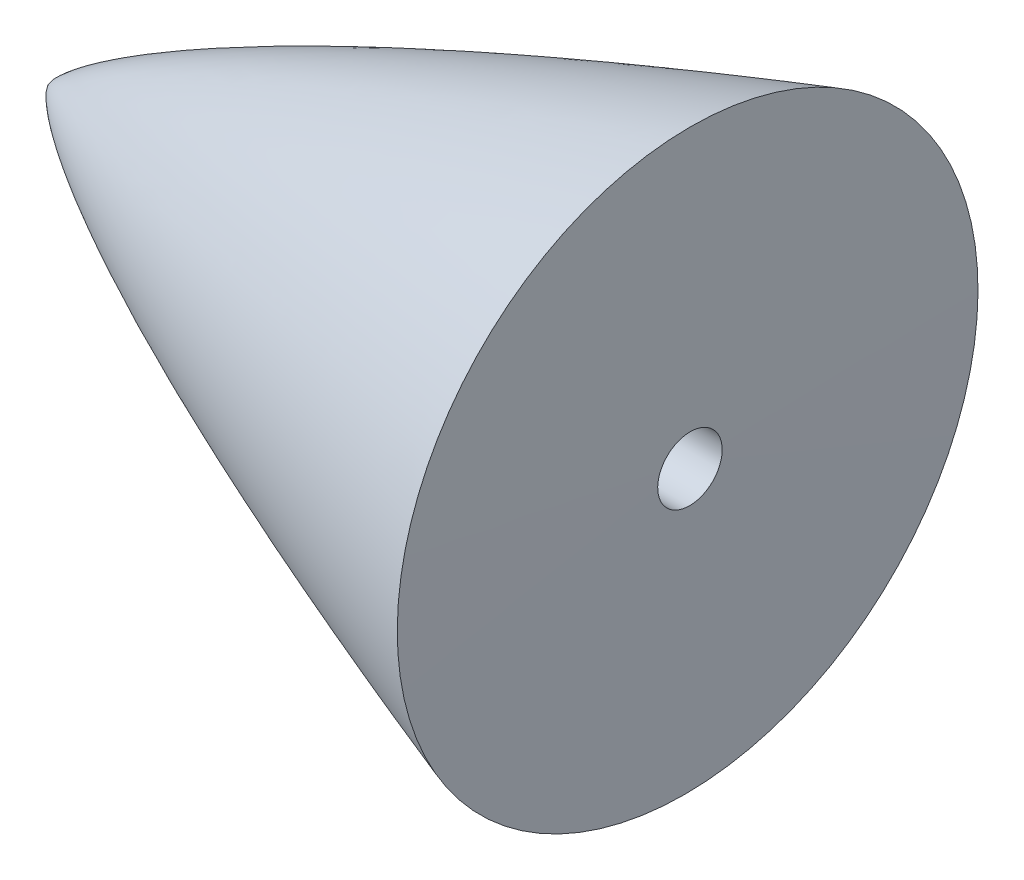
SolidWorks part; units mm, degrees
ref_plane "Front Plane" through (0, 0, 0) normal (0, 0, 1) x (1, 0, 0)
ref_plane "Top Plane" through (0, 0, 0) normal (0, 1, 0) x (1, 0, 0)
ref_plane "Right Plane" through (0, 0, 0) normal (1, 0, 0) x (0, 0, -1)
sketch "Sketch1" plane through (0, 0, 0) normal (0, 0, 1) x (1, 0, 0)
  line L0 (0, 0) -> (50.8, -0.4644)
  line L1 (50.8, -0.4644) -> (50.8, 22.5304)
  spline S0 degree 4 poles (0, 0) (0.0034, 0.018) (0.0111, 0.0443) (0.0276, 0.0824) (0.0564, 0.1398) (0.0969, 0.2096) (0.165, 0.3125) (0.2783, 0.4621) (0.4613, 0.6747) (0.7551, 0.9759) (1.2208, 1.3985) (1.948, 1.9843) (3.0376, 2.7663) (4.6883, 3.8283) (7.0687, 5.2032) (10.0936, 6.7823) (13.6413, 8.4827) (17.4617, 10.1905) (21.314, 11.8194) (25.1956, 13.386) (28.6053, 14.7087) (31.5467, 15.8166) (33.9916, 16.7185) (35.9736, 17.4379) (37.9137, 18.1333) (39.9342, 18.8455) (42.317, 19.6776) (44.945, 20.576) (47.1774, 21.3311) (50.1657, 22.3229) (51.8907, 22.8893) (54.2047, 23.6424) (55.1287, 23.9372) (55.9178, 24.1913) knots 0 0 0 0 0 0.00119 0.001793 0.002702 0.004188 0.006457 0.009843 0.01494 0.022485 0.033904 0.050863 0.075851 0.109982 0.161962 0.230225 0.298488 0.366751 0.435014 0.503277 0.57154 0.605671 0.639803 0.673934 0.708066 0.742197 0.776328 0.844591 0.878723 0.912854 0.956427 1 1 1 1 1 construction
  spline S1 degree 4 poles (0, 0) (0.0034, 0.018) (0.0111, 0.0443) (0.0276, 0.0824) (0.0564, 0.1398) (0.0969, 0.2096) (0.165, 0.3125) (0.2783, 0.4621) (0.4613, 0.6747) (0.7551, 0.9759) (1.2208, 1.3985) (1.948, 1.9843) (3.0376, 2.7663) (4.6883, 3.8283) (7.0687, 5.2032) (10.0936, 6.7823) (13.6413, 8.4827) (17.4617, 10.1905) (21.314, 11.8194) (25.1956, 13.386) (28.6053, 14.7087) (31.5467, 15.8166) (33.9916, 16.7185) (35.9736, 17.4379) (37.9137, 18.1333) (39.9342, 18.8455) (42.317, 19.6776) (44.945, 20.576) (47.1774, 21.3311) (49.4427, 22.0829) (50.3465, 22.3813) (50.8, 22.5304) knots 0 0 0 0 0 0.00119 0.001793 0.002702 0.004188 0.006457 0.009843 0.01494 0.022485 0.033904 0.050863 0.075851 0.109982 0.161962 0.230225 0.298488 0.366751 0.435014 0.503277 0.57154 0.605671 0.639803 0.673934 0.708066 0.742197 0.776328 0.844591 0.878723 0.912854 0.912854 0.912854 0.912854 0.912854
  point P0 (0, 0)
  dimension "D1" = 50.8
  dimension "D2" = 22.9948
revolve "Revolve3" add sketch "Sketch1" angle 360 about L0
ref_plane "Plane1" through (50.7915, -0.9288, 0) normal (0.9998, -0.0183, 0) x (0, 0, -1)
sketch "Sketch3" plane through (50.7915, -0.9288, 0) normal (0.9998, -0.0183, 0) x (0, 0, -1)
  line L0 (-24.6013, 0) -> (21.3252, 0) construction
  line L1 (0, -23.733) -> (0, 23.9549) construction
hole_wizard "1/4-20 Tapped Hole2" positions "3DSketch4" profile "Sketch5" tap size "1/4-20" standard "ANSI Inch"
sketch3d "3DSketch4"
  line L0 (50.7915, -0.9288, 24.6013) -> (50.7915, -0.9288, -21.3252) construction
  point P0 (50.7915, -0.9288, 0)
sketch "Sketch5" plane through (50.7915, -0.9288, 0) normal (0.0129, 0.707, 0.707) x (0.0129, 0.7069, -0.7072)
  line L0 (0, 0) -> (0, 26.9338)
  line L1 (0, 26.9338) -> (2.5527, 25.4)
  line L2 (2.5527, 25.4) -> (2.5527, 0)
  line L5 (2.5527, 0) -> (0, 0)
  line L10 (0, 26.9338) -> (-2.5527, 25.4) construction
  line L11 (0, -6.35) -> (0, 107.95) construction
  dimension "Tap Drill Dia." = 5.1054
  dimension "Tap Drill Depth" = 25.4
  dimension "Drill Angle" = 118
cosmetic thread "Hole Thread1" parameters "D1"=12.7, "D2"=6.35
